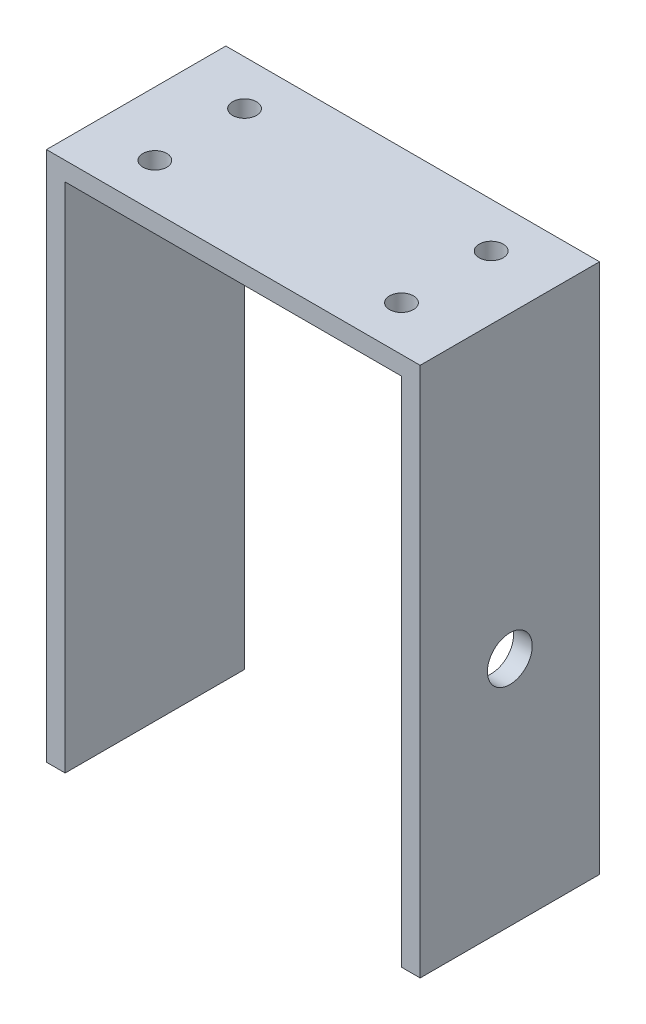
SolidWorks part; units mm, degrees
material "1060 合金"
ref_plane "正面" through (0, 0, 0) normal (0, 0, 1) x (1, 0, 0)
ref_plane "平面" through (0, 0, 0) normal (0, 1, 0) x (1, 0, 0)
ref_plane "右側面" through (0, 0, 0) normal (1, 0, 0) x (0, 0, -1)
sketch "ｽｹｯﾁ1" plane through (0, 0, 0) normal (0, 0, 1) x (1, 0, 0)
  line L0 (-22.5, 47.5) -> (22.5, 47.5)
  line L1 (-25, 50) -> (25, 50)
  line L2 (-25, 50) -> (-25, -50)
  line L3 (-25, -50) -> (25, -50)
  line L4 (25, 50) -> (25, -50)
  line L5 (-25, 50) -> (25, -50) construction
  line L6 (-25, -50) -> (25, 50) construction
  line L7 (22.5, 47.5) -> (22.5, -47.5)
  line L8 (-22.5, -47.5) -> (22.5, -47.5)
  line L9 (-22.5, 47.5) -> (-22.5, -47.5)
  point P0 (0, 0)
  dimension "D2" = 100
  dimension "D3" = 50
  dimension "D1" = 2.5
extrude "ﾎﾞｽ - 押し出し1" add sketch "ｽｹｯﾁ1" along normal blind 24
sketch "ｽｹｯﾁ3" plane through (0, 50, 0) normal (0, 1, 0) x (1, 0, 0)
  line L1 (-25, -24) -> (-25, 0) construction
  line L2 (25, 0) -> (-25, 0) construction
  circle A0 centre (-16.5, -6) radius 1.6
  circle A1 centre (16.5, -6) radius 1.6
  circle A2 centre (16.5, -18) radius 1.6
  circle A3 centre (-16.5, -18) radius 1.6
  dimension "D1" = 33
  dimension "D2" = 8.5
  dimension "D3" = 3.2
  dimension "D4" = 6
  dimension "D6" = 12
  dimension "D5" = 2
extrude "ｶｯﾄ - 押し出し2" cut sketch "ｽｹｯﾁ3" against normal through all and the other way through all
sketch "ｽｹｯﾁ4" plane through (25, 0, 0) normal (1, 0, 0) x (0, 0, -1)
  line L1 (-24, -50) -> (-24, 50) construction
  line L2 (-24, -50) -> (0, -50) construction
  circle A0 centre (-12, 10) radius 3
  circle A1 centre (-12, -30) radius 4
  dimension "D1" = 6
  dimension "D2" = 20
  dimension "D3" = 40
  dimension "D4" = 12
  dimension "D5" = 8
extrude "ｶｯﾄ - 押し出し3" cut sketch "ｽｹｯﾁ4" against normal up to next and the other way through all
sketch "ｽｹｯﾁ5" plane through (0, -50, 0) normal (0, -1, 0) x (1, 0, 0)
  line L4 (-25, 0) -> (25, 0)
  line L5 (25, 0) -> (25, 24)
  line L6 (25, 24) -> (-25, 24)
  line L7 (-25, 24) -> (-25, 0)
  line L8 (-25, 0) -> (25, 0)
  line L9 (25, 0) -> (25, 24)
  line L10 (25, 24) -> (-25, 24)
  line L11 (-25, 24) -> (-25, 0)
  dimension "D1" = 0
extrude "ｶｯﾄ - 押し出し4" cut sketch "ｽｹｯﾁ5" against normal blind 29
